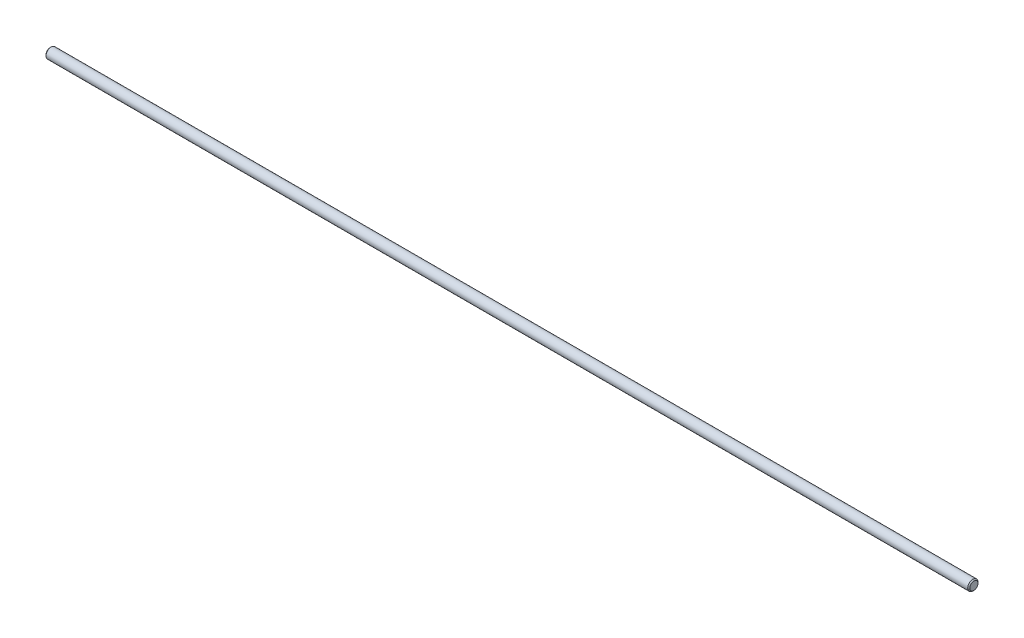
SolidWorks part; units mm, degrees
material "Plain Carbon Steel"
ref_plane "Front" through (0, 0, 0) normal (0, 0, 1) x (1, 0, 0)
ref_plane "Top" through (0, 0, 0) normal (0, 1, 0) x (1, 0, 0)
ref_plane "Right" through (0, 0, 0) normal (1, 0, 0) x (0, 0, -1)
sketch "Sketch1" plane through (0, 0, 0) normal (1, 0, 0) x (0, 0, -1)
  circle A0 centre (0, 0) radius 2.5
  dimension "D1" = 5
extrude "Boss-Extrude1" add sketch "Sketch1" along normal blind 450
chamfer "Chamfer1" distance 0.5 angle 45 2 edges at (450, 0, -2.5) (0, 0, -2.5)
